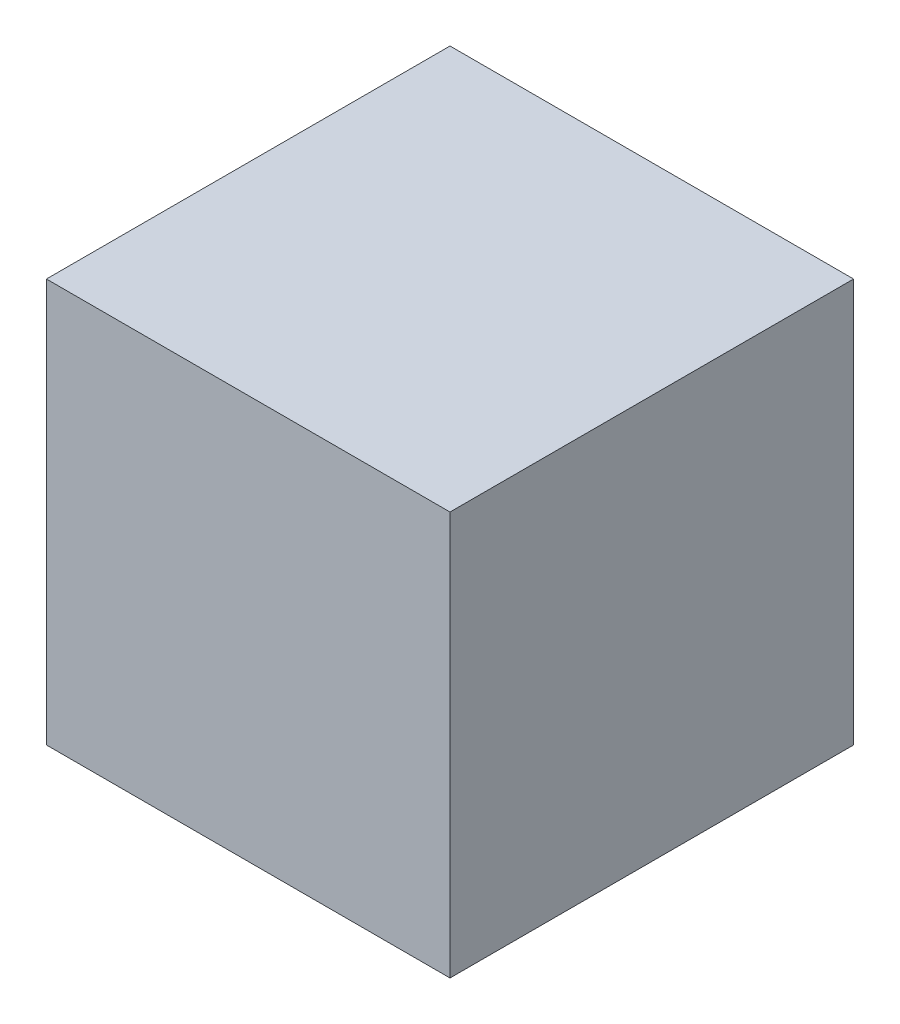
SolidWorks part; units mm, degrees
ref_plane "Front Plane" through (0, 0, 0) normal (0, 0, 1) x (1, 0, 0)
ref_plane "Top Plane" through (0, 0, 0) normal (0, 1, 0) x (1, 0, 0)
ref_plane "Right Plane" through (0, 0, 0) normal (1, 0, 0) x (0, 0, -1)
sketch "Sketch1" plane through (0, 0, 0) normal (0, 0, 1) x (1, 0, 0)
  line L0 (0, 0) -> (50, 0)
  line L1 (50, 0) -> (50, 50)
  line L2 (50, 50) -> (0, 50)
  line L3 (0, 50) -> (0, 0)
extrude "Boss-Extrude1" add sketch "Sketch1" along normal blind 50
